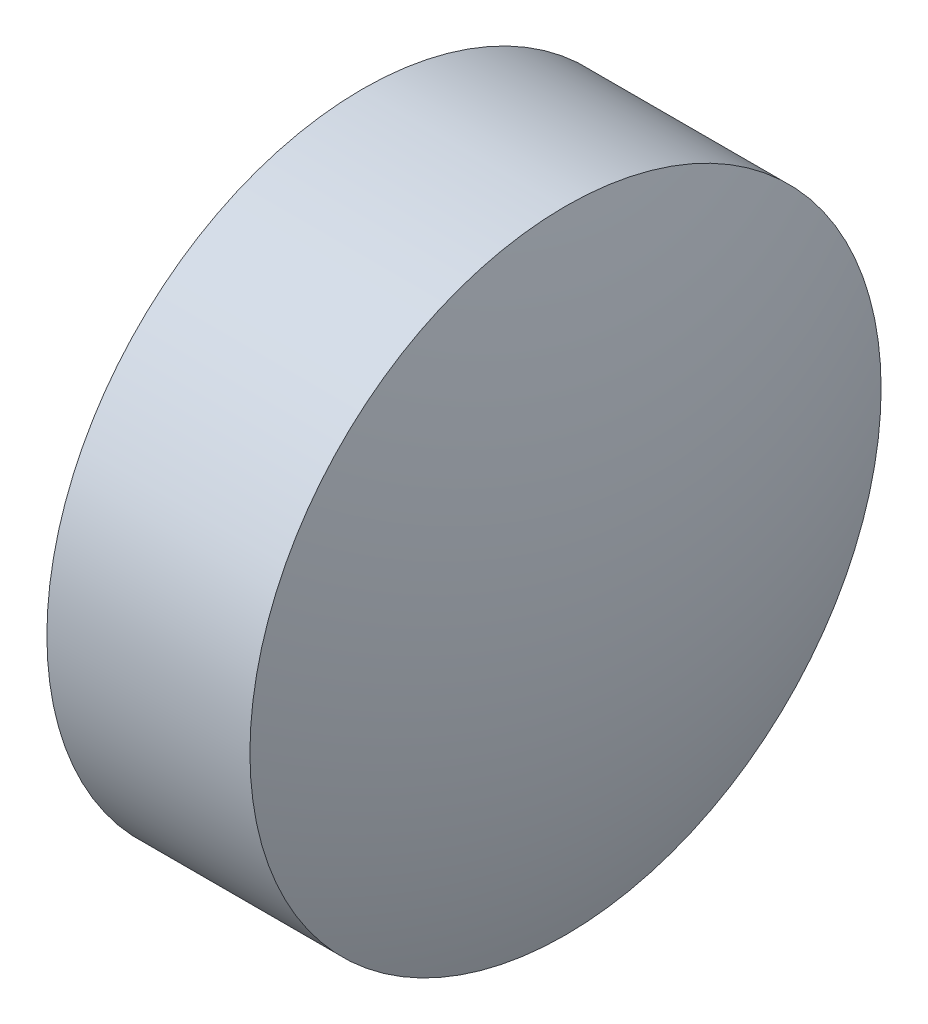
SolidWorks part; units mm, degrees
ref_plane "前视基准面" through (0, 0, 0) normal (0, 0, 1) x (1, 0, 0)
ref_plane "上视基准面" through (0, 0, 0) normal (0, 1, 0) x (1, 0, 0)
ref_plane "右视基准面" through (0, 0, 0) normal (1, 0, 0) x (0, 0, -1)
sketch "草图1" plane through (0, 0, 0) normal (0, 0, 1) x (1, 0, 0)
  line L0 (17.3949, 11.4841) -> (23.5603, 11.4841) construction
  line L1 (19.4582, 14.4841) -> (21.3882, 14.4841)
  line L2 (21.3882, 14.4841) -> (21.3882, 8.4841)
  line L3 (21.3882, 8.4841) -> (19.4582, 8.4841)
  line L4 (19.4582, 8.4841) -> (19.4582, 14.4841)
  arc A0 (19.4582, 14.4841) -> (19.4582, 8.4841) centre (27.602, 11.4841) ccw
  arc A1 (21.3882, 8.4841) -> (21.3882, 14.4841) centre (13.2444, 11.4841) ccw
  dimension "D1" = 6
  dimension "D2" = 1.93
revolve "旋转1" add sketch "草图1" angle 360 about L0
